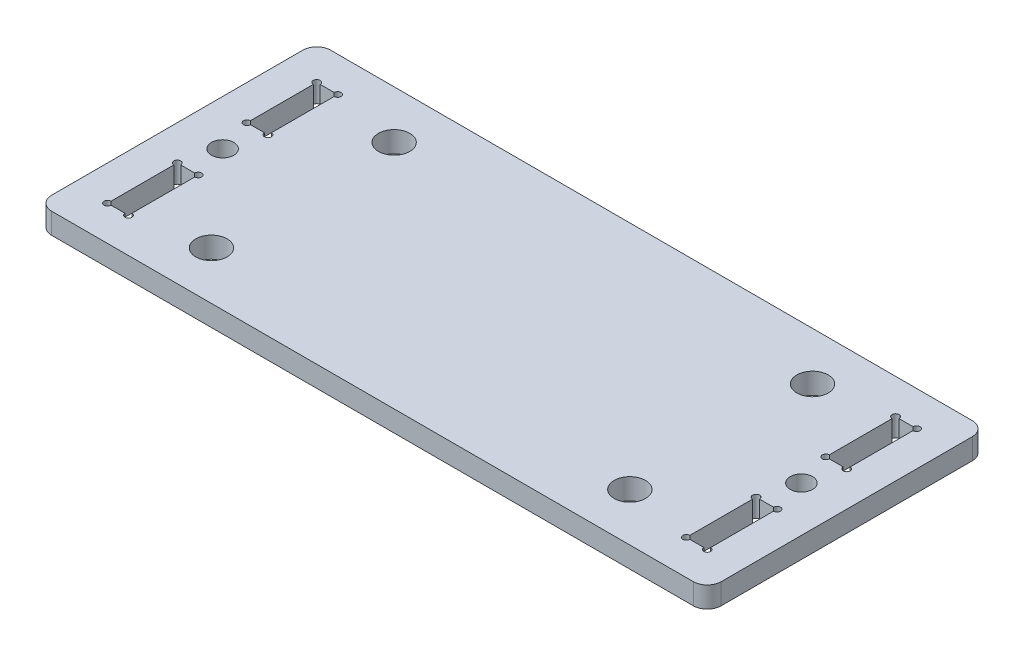
SolidWorks part; units mm, degrees
material "Acrylic (Medium-high impact)"
ref_plane "Front Plane" through (0, 0, 0) normal (0, 0, 1) x (1, 0, 0)
ref_plane "Top Plane" through (0, 0, 0) normal (0, 1, 0) x (1, 0, 0)
ref_plane "Right Plane" through (0, 0, 0) normal (1, 0, 0) x (0, 0, -1)
sketch "Sketch1" plane through (0, 0, 0) normal (0, 1, 0) x (1, 0, 0)
  line L0 (-30, 13.1) -> (30, -13.1) construction
  line L1 (-46, -20) -> (46, -20)
  line L2 (-48, -18) -> (-48, 18)
  line L4 (48, -18) -> (48, 18)
  line L5 (-48, -20) -> (48, 20) construction
  line L6 (-48, 20) -> (48, -20) construction
  line L7 (-30, 13.1) -> (-30, -13.1) construction
  line L8 (-30, -13.1) -> (30, -13.1) construction
  line L9 (30, -13.1) -> (30, 13.1) construction
  line L10 (-30, 13.1) -> (30, 13.1) construction
  line L11 (30, 13.1) -> (-30, -13.1) construction
  line L18 (-46, 20) -> (46, 20)
  line L20 (-41.5, 0) -> (41.5, 0) construction
  line L21 (-43, 15) -> (-40, 15)
  line L22 (-43, 15) -> (-43, 5)
  line L23 (-43, 5) -> (-40, 5)
  line L24 (-40, 15) -> (-40, 5)
  line L25 (-43, 15) -> (-40, 5) construction
  line L26 (-43, 5) -> (-40, 15) construction
  line L27 (-43, -5) -> (-40, -5)
  line L28 (-43, -5) -> (-43, -15)
  line L29 (-43, -15) -> (-40, -15)
  line L30 (-40, -5) -> (-40, -15)
  line L31 (-43, -5) -> (-40, -15) construction
  line L32 (-43, -15) -> (-40, -5) construction
  line L33 (40, 15) -> (43, 15)
  line L34 (40, 15) -> (40, 5)
  line L35 (40, 5) -> (43, 5)
  line L36 (43, 15) -> (43, 5)
  line L37 (40, 15) -> (43, 5) construction
  line L38 (40, 5) -> (43, 15) construction
  line L39 (40, -5) -> (43, -5)
  line L40 (40, -5) -> (40, -15)
  line L41 (40, -15) -> (43, -15)
  line L42 (43, -5) -> (43, -15)
  line L43 (40, -5) -> (43, -15) construction
  line L44 (40, -15) -> (43, -5) construction
  line L45 (-43, -5) -> (-40, 5) construction
  line L46 (40, 5) -> (43, -5) construction
  circle A0 centre (-30, 13.1) radius 2.25
  circle A1 centre (30, 13.1) radius 2.25
  circle A2 centre (30, -13.1) radius 2.25
  circle A3 centre (-30, -13.1) radius 2.25
  circle A4 centre (41.5, 0) radius 1.6
  circle A5 centre (-41.5, 0) radius 1.6
  arc A6 (-48, -18) -> (-46, -20) centre (-46, -18) ccw
  arc A7 (46, -20) -> (48, -18) centre (46, -18) ccw
  arc A8 (48, 18) -> (46, 20) centre (46, 18) ccw
  arc A9 (-46, 20) -> (-48, 18) centre (-46, 18) ccw
  point P0 (0, 0)
  point P20 (-41.5, 10)
  point P23 (-41.5, -10)
  point P28 (41.5, 10)
  point P33 (41.5, -10)
  dimension "D5" = 4.5
  dimension "D9" = 3.2
  dimension "D10" = 10
  dimension "D13" = 2
  dimension "D14" = 2
  dimension "D15" = 2
  dimension "D16" = 2
  dimension "D1" = 3
  dimension "D2" = 40
  dimension "D6" = 60
  dimension "D7" = 26.2
  dimension "D8" = 80
  dimension "D11" = 10
  dimension "D12" = 5
  dimension "D3" = 2
  dimension "D4" = 2
extrude "Boss-Extrude1" add sketch "Sketch1" along normal blind 3
sketch "Sketch2" plane through (0, 3, 0) normal (0, 1, 0) x (1, 0, 0)
  circle A4 centre (-43, 15) radius 0.5
  circle A5 centre (-40, 15) radius 0.5
  circle A6 centre (-40, 5) radius 0.5
  circle A7 centre (-43, 5) radius 0.5
  circle A8 centre (-43, -5) radius 0.5
  circle A9 centre (-40, -5) radius 0.5
  circle A10 centre (-43, -15) radius 0.5
  circle A11 centre (-40, -15) radius 0.5
  circle A12 centre (40, -15) radius 0.5
  circle A13 centre (43, -15) radius 0.5
  circle A14 centre (43, -5) radius 0.5
  circle A15 centre (40, -5) radius 0.5
  circle A16 centre (40, 5) radius 0.5
  circle A17 centre (43, 5) radius 0.5
  circle A18 centre (43, 15) radius 0.5
  circle A19 centre (40, 15) radius 0.5
  dimension "D1" = 1
extrude "Cut-Extrude1" cut sketch "Sketch2" against normal through all
